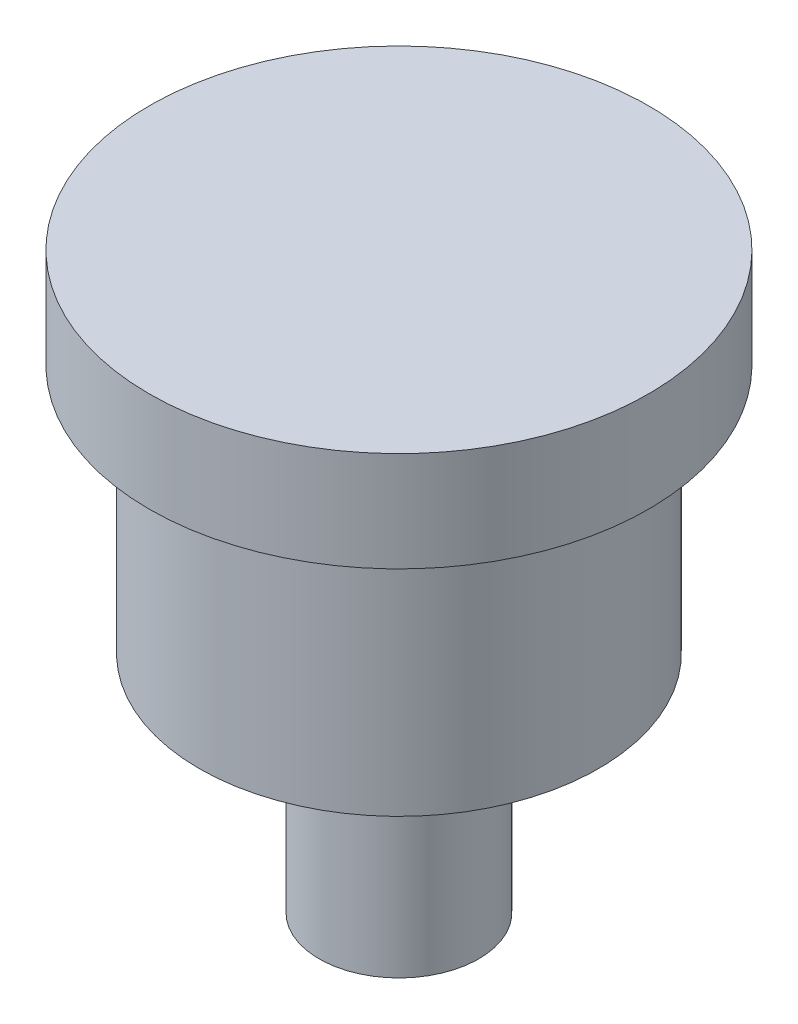
SolidWorks part; units mm, degrees
ref_plane "Front Plane" through (0, 0, 0) normal (0, 0, 1) x (1, 0, 0)
ref_plane "Top Plane" through (0, 0, 0) normal (0, 1, 0) x (1, 0, 0)
ref_plane "Right Plane" through (0, 0, 0) normal (1, 0, 0) x (0, 0, -1)
sketch "Sketch1" plane through (0, 0, 0) normal (0, 1, 0) x (1, 0, 0)
  circle A0 centre (0, 0) radius 5
  dimension "D1" = 10
extrude "Boss-Extrude1" add sketch "Sketch1" along normal blind 2
sketch "Sketch6" plane through (0, 0, 0) normal (0, -1, 0) x (-1, 0, 0)
  circle A0 centre (0, 0) radius 4
  dimension "D1" = 8
extrude "Boss-Extrude4" add sketch "Sketch6" along normal blind 5
sketch "Sketch4" plane through (0, -5, 0) normal (0, -1, 0) x (-1, 0, 0)
  circle A0 centre (0, 0) radius 1.6
  dimension "D1" = 3.2
extrude "Boss-Extrude5" add sketch "Sketch4" along normal blind 4.5
